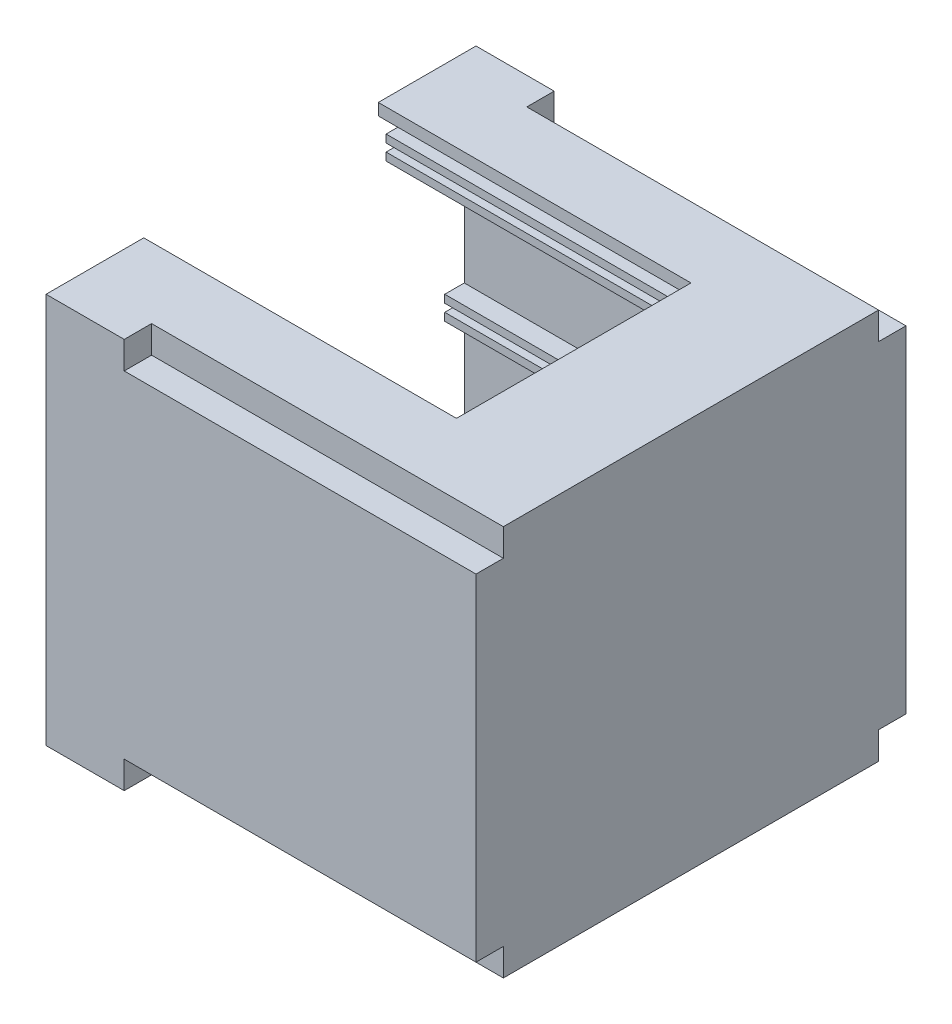
SolidWorks part; units mm, degrees
ref_plane "Front Plane" through (0, 0, 0) normal (0, 0, 1) x (1, 0, 0)
ref_plane "Top Plane" through (0, 0, 0) normal (0, 1, 0) x (1, 0, 0)
ref_plane "Right Plane" through (0, 0, 0) normal (1, 0, 0) x (0, 0, -1)
sketch "Sketch2" plane through (0, 0, 0) normal (0, 1, 0) x (1, 0, 0)
  line L1 (0, 0) -> (110, 0)
  line L2 (0, 0) -> (0, 110)
  line L3 (0, 110) -> (110, 110)
  line L4 (110, 0) -> (110, 110)
  dimension "D1" = 110
  dimension "D2" = 110
extrude "Boss-Extrude1" add sketch "Sketch2" along normal blind 100
sketch "Sketch3" plane through (0, 0, 0) normal (-1, 0, 0) x (0, 0, 1)
  line L0 (-110, 100) -> (0, 0) construction
  line L1 (-110, 0) -> (0, 100) construction
  line L2 (-110, 100) -> (0, 100) construction
  line L3 (-107, 3) -> (-3, 3)
  line L4 (-107, 3) -> (-107, 97)
  line L5 (-107, 97) -> (-3, 97)
  line L6 (-3, 3) -> (-3, 97)
  line L7 (-107, 3) -> (-3, 97) construction
  line L8 (-107, 97) -> (-3, 3) construction
  line L9 (0, 100) -> (0, 0) construction
  point P8 (-55, 50)
  dimension "D1" = 3
  dimension "D2" = 3
extrude "Cut-Extrude1" cut sketch "Sketch3" against normal blind 107
sketch "Sketch4" plane through (0, 100, 0) normal (0, 1, 0) x (1, 0, 0)
  line L0 (0, 110) -> (0, 0) construction
  line L1 (0, 85) -> (80, 85)
  line L2 (0, 85) -> (0, 25)
  line L3 (0, 25) -> (80, 25)
  line L4 (80, 85) -> (80, 25)
  line L5 (110, 110) -> (0, 110) construction
  line L6 (0, 0) -> (110, 0) construction
  line L7 (110, 0) -> (110, 110) construction
  dimension "D1" = 25
  dimension "D2" = 25
  dimension "D3" = 30
extrude "Cut-Extrude2" cut sketch "Sketch4" against normal blind 10
sketch "Sketch5" plane through (107, 0, 0) normal (-1, 0, 0) x (0, 0, 1)
  line L0 (-107, 97) -> (-107, 3) construction
  line L1 (-107, 92) -> (-87, 92)
  line L2 (-107, 92) -> (-107, 86)
  line L3 (-107, 86) -> (-87, 86)
  line L4 (-87, 92) -> (-87, 86)
  line L5 (-3, 3) -> (-3, 97) construction
  line L6 (-3, 92) -> (-23, 92)
  line L7 (-3, 92) -> (-3, 86)
  line L8 (-3, 86) -> (-23, 86)
  line L9 (-23, 92) -> (-23, 86)
  line L10 (-3, 97) -> (-107, 97) construction
  line L11 (-3, 97) -> (-25, 97) construction
  dimension "D1" = 5
  dimension "D2" = 6
  dimension "D3" = 20
  dimension "D4" = 5
  dimension "D5" = 6
  dimension "D6" = 20
extrude "Boss-Extrude2" add sketch "Sketch5" along normal blind 107
sketch "Sketch6" plane through (0, 0, 0) normal (-1, 0, 0) x (0, 0, 1)
  line L0 (-87, 86) -> (-87, 92) construction
  line L1 (-87, 90) -> (-92, 90)
  line L2 (-87, 90) -> (-87, 88)
  line L3 (-87, 88) -> (-92, 88)
  line L4 (-92, 90) -> (-92, 88)
  line L6 (-23, 92) -> (-23, 86) construction
  line L7 (-23, 90) -> (-18, 90)
  line L8 (-23, 90) -> (-23, 88)
  line L9 (-23, 88) -> (-18, 88)
  line L10 (-18, 90) -> (-18, 88)
  line L11 (-87, 92) -> (-107, 92) construction
  line L12 (-107, 86) -> (-87, 86) construction
  line L13 (-3, 92) -> (-23, 92) construction
  line L14 (-23, 86) -> (-3, 86) construction
  line L15 (-87, 86) -> (-87, 92) construction
  line L16 (-23, 92) -> (-23, 86) construction
  dimension "D1" = 2
  dimension "D2" = 2
  dimension "D3" = 2
  dimension "D4" = 2
  dimension "D5" = 5
  dimension "D6" = 5
extrude "Cut-Extrude3" cut sketch "Sketch6" against normal blind 107
sketch "Sketch7" plane through (107, 0, 0) normal (-1, 0, 0) x (0, 0, 1)
  line L0 (-107, 86) -> (-107, 3) construction
  line L1 (-3, 3) -> (-3, 86) construction
  line L2 (-107, 14) -> (-82, 14)
  line L3 (-107, 14) -> (-107, 8)
  line L4 (-107, 8) -> (-82, 8)
  line L5 (-82, 14) -> (-82, 8)
  line L6 (-3, 14) -> (-28, 14)
  line L7 (-3, 14) -> (-3, 8)
  line L8 (-3, 8) -> (-28, 8)
  line L9 (-28, 14) -> (-28, 8)
  line L10 (-107, 3) -> (-3, 3) construction
  line L11 (-107, 49) -> (-102, 49)
  line L12 (-107, 49) -> (-107, 43)
  line L13 (-107, 43) -> (-102, 43)
  line L14 (-102, 49) -> (-102, 43)
  line L15 (-3, 49) -> (-8, 49)
  line L16 (-3, 49) -> (-3, 43)
  line L17 (-3, 43) -> (-8, 43)
  line L18 (-8, 49) -> (-8, 43)
  line L19 (-107, 3) -> (-3, 3) construction
  dimension "D1" = 5
  dimension "D2" = 6
  dimension "D3" = 5
  dimension "D4" = 6
  dimension "D5" = 6
  dimension "D6" = 6
  dimension "D7" = 5
  dimension "D8" = 5
  dimension "D9" = 40
  dimension "D10" = 40
  dimension "D11" = 25
  dimension "D12" = 25
extrude "Boss-Extrude3" add sketch "Sketch7" along normal blind 107
sketch "Sketch8" plane through (0, 0, 0) normal (-1, 0, 0) x (0, 0, 1)
  line L5 (-8, 49) -> (-8, 43) construction
  line L6 (-8, 47) -> (-3, 47)
  line L7 (-8, 47) -> (-8, 45)
  line L8 (-8, 45) -> (-3, 45)
  line L9 (-3, 47) -> (-3, 45)
  line L10 (-82, 8) -> (-82, 14) construction
  line L11 (-82, 12) -> (-87, 12)
  line L12 (-82, 12) -> (-82, 10)
  line L13 (-82, 10) -> (-87, 10)
  line L14 (-87, 12) -> (-87, 10)
  line L15 (-28, 14) -> (-28, 8) construction
  line L16 (-28, 12) -> (-23, 12)
  line L17 (-28, 12) -> (-28, 10)
  line L18 (-28, 10) -> (-23, 10)
  line L19 (-23, 12) -> (-23, 10)
  line L29 (-102, 43) -> (-102, 49) construction
  line L30 (-102, 45) -> (-107, 45)
  line L31 (-102, 45) -> (-102, 47)
  line L32 (-102, 47) -> (-107, 47)
  line L33 (-107, 45) -> (-107, 47)
  line L34 (-102, 49) -> (-107, 49) construction
  line L35 (-3, 49) -> (-8, 49) construction
  line L36 (-82, 14) -> (-107, 14) construction
  line L37 (-107, 8) -> (-82, 8) construction
  line L38 (-3, 14) -> (-28, 14) construction
  line L39 (-28, 8) -> (-3, 8) construction
  dimension "D1" = 2
  dimension "D2" = 2
  dimension "D3" = 5
  dimension "D4" = 5
  dimension "D5" = 2
  dimension "D6" = 2
  dimension "D7" = 2
  dimension "D8" = 2
  dimension "D9" = 5
  dimension "D10" = 2
  dimension "D11" = 2
  dimension "D12" = 5
extrude "Cut-Extrude4" cut sketch "Sketch8" against normal blind 107
sketch "Sketch9" plane through (110, 0, 0) normal (1, 0, 0) x (0, 0, -1)
  line L14 (0, 0) -> (10, 0)
  line L15 (0, 0) -> (0, 10)
  line L16 (0, 10) -> (10, 10)
  line L17 (10, 0) -> (10, 10)
  line L18 (110, 0) -> (100, 0)
  line L19 (110, 0) -> (110, 10)
  line L20 (110, 10) -> (100, 10)
  line L21 (100, 0) -> (100, 10)
  line L22 (110, 100) -> (100, 100)
  line L23 (110, 100) -> (110, 90)
  line L24 (110, 90) -> (100, 90)
  line L25 (100, 100) -> (100, 90)
  line L26 (0, 100) -> (10, 100)
  line L27 (0, 100) -> (0, 90)
  line L28 (0, 90) -> (10, 90)
  line L29 (10, 100) -> (10, 90)
  dimension "D1" = 10
  dimension "D2" = 10
  dimension "7" = 10
  dimension "D4" = 10
  dimension "D5" = 10
  dimension "D6" = 10
  dimension "D7" = 10
  dimension "D8" = 10
extrude "Boss-Extrude4" add sketch "Sketch9" against normal blind 110
sketch "Sketch11" plane through (110, 0, 0) normal (1, 0, 0) x (0, 0, -1)
  line L1 (0, 100) -> (7, 100)
  line L2 (0, 100) -> (0, 93)
  line L3 (0, 93) -> (7, 93)
  line L4 (7, 100) -> (7, 93)
  line L5 (110, 100) -> (103, 100)
  line L6 (110, 100) -> (110, 93)
  line L7 (110, 93) -> (103, 93)
  line L8 (103, 100) -> (103, 93)
  line L9 (0, 0) -> (7, 0)
  line L10 (0, 0) -> (0, 7)
  line L11 (0, 7) -> (7, 7)
  line L12 (7, 0) -> (7, 7)
  line L13 (110, 0) -> (103, 0)
  line L14 (110, 0) -> (110, 7)
  line L15 (110, 7) -> (103, 7)
  line L16 (103, 0) -> (103, 7)
  dimension "D1" = 7
  dimension "D2" = 7
  dimension "D3" = 7
  dimension "D4" = 7
  dimension "D5" = 7
  dimension "D6" = 7
  dimension "D7" = 7
  dimension "D8" = 7
extrude "Cut-Extrude5" cut sketch "Sketch11" against normal blind 90
sketch "Sketch13" plane through (0, 0, 0) normal (-1, 0, 0) x (0, 0, 1)
  line L0 (-110, 100) -> (-85, 100) construction
  line L1 (-110, 100) -> (-110, 0) construction
  line L2 (-25, 100) -> (0, 100) construction
  line L3 (0, 100) -> (0, 0) construction
  line L4 (-110, 0) -> (0, 0) construction
  circle A0 centre (-106.5, 3.5) radius 1.5
  circle A1 centre (-3.5, 96.5) radius 1.5
  circle A2 centre (-106.5, 96.5) radius 1.5
  circle A3 centre (-3.5, 3.5) radius 1.5
  point P4 (-105.4904, 5.9677)
  point P7 (-105.4904, 95.2065)
  point P8 (-4.7705, 94.2933)
  point P11 (-4.7705, 5.9677)
  dimension "D1" = 3
  dimension "D4" = 3
  dimension "D7" = 3
  dimension "D10" = 3
  dimension "D2" = 3.5
  dimension "D3" = 3.5
  dimension "D5" = 3.5
  dimension "D6" = 3.5
  dimension "D8" = 3.5
  dimension "D9" = 3.5
  dimension "D11" = 3.5
  dimension "D12" = 3.5
extrude "Cut-Extrude6" cut sketch "Sketch13" against normal blind 19
